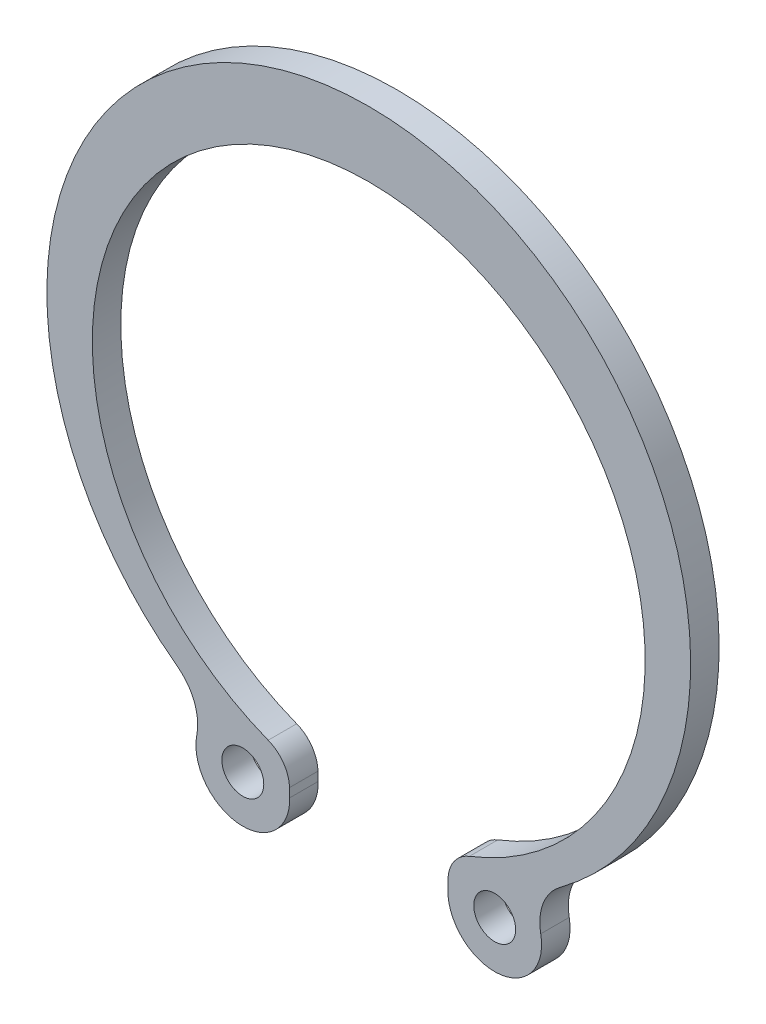
SolidWorks part; units mm, degrees
ref_plane "Спереди" through (0, 0, 0) normal (0, 0, 1) x (1, 0, 0)
ref_plane "Сверху" through (0, 0, 0) normal (0, 1, 0) x (1, 0, 0)
ref_plane "Справа" through (0, 0, 0) normal (1, 0, 0) x (0, 0, -1)
sketch "Эскиз1" plane through (0, 0, 0) normal (0, 0, 1) x (1, 0, 0)
  line L0 (0, -1000) -> (0, 49000) construction
  line L1 (5, -17.2154) -> (5, -16.6916)
  arc A0 (6.2265, -14.8472) -> (0, 16.1) centre (0, 0) ccw
  circle A2 centre (0, 0) radius 17.5 construction
  circle A3 centre (0, 0) radius 23.6 construction
  circle A4 centre (0, 0) radius 16.5 construction
  circle A5 centre (7.8, -17.2154) radius 1.25
  arc A7 (5, -17.2154) -> (10.5324, -16.6038) centre (7.8, -17.2154) ccw
  arc A8 (11.6077, -13.5886) -> (10.5324, -16.6038) centre (13.4599, -15.9485) ccw
  arc A9 (6.2265, -14.8472) -> (5, -16.6916) centre (7, -16.6916) ccw
  arc A10 (11.6077, -13.5886) -> (0, 20) centre (0, 1.2) ccw
  circle A12 centre (0, 1.2) radius 18.8 construction
  dimension "_d2" = 32.2
  dimension "_d3" = 37.6
  dimension "_d" = 35
  dimension "_D_" = 47.2
  dimension "_d1" = 33
  dimension "_d4" = 2.5
  dimension "_a" = 5.6
  dimension "_r1" = 3
  dimension "_r2" = 2
  dimension "_e" = 1.2
  dimension "_l" = 5
sketch "Эскиз2" plane through (0, 0, 0) normal (0, 0, 1) x (1, 0, 0)
  line L0 (0, -201000) -> (0, 249000) construction
  line L1 (0, -998.9795) -> (0, 49001.0205) construction
  line L2 (0, 0) -> (6.2265, -14.8472) construction
  line L3 (0, 0) -> (-6.0026, -15.3694) construction
  line L4 (0, 16.5) -> (0, 20.4)
  line L5 (6.2265, -14.8472) -> (5, -16.6916) construction
  line L6 (-6.0026, -15.3694) -> (-4.7308, -17.1829) construction
  line L7 (-4.7308, -17.1829) -> (-4.7178, -17.7065)
  line L8 (5, -17.2154) -> (5, -16.6916) construction
  line L9 (-11.4266, -14.2593) -> (-10.2657, -17.2426) construction
  line L10 (11.6077, -13.5886) -> (10.5324, -16.6038) construction
  line L11 (0, 20.4) -> (1.7, 20.4) construction
  arc A0 (0, 16.5) -> (-6.0026, -15.3694) centre (0, 0) ccw
  circle A1 centre (0, 0) radius 16.5 construction
  circle A2 centre (-7.517, -17.776) radius 1.25
  circle A3 centre (7.8, -17.2154) radius 1.25 construction
  arc A4 (-10.2657, -17.2426) -> (-4.7178, -17.7065) centre (-7.517, -17.776) ccw
  arc A5 (5, -17.2154) -> (10.5324, -16.6038) centre (7.8, -17.2154) ccw construction
  arc A6 (-6.0026, -15.3694) -> (-4.7308, -17.1829) centre (-6.7302, -17.2324) cw
  arc A7 (6.2265, -14.8472) -> (5, -16.6916) centre (7, -16.6916) ccw construction
  arc A8 (0, 20.4) -> (-11.4266, -14.2593) centre (0, 1.1868) ccw
  arc A9 (-10.2657, -17.2426) -> (-11.4266, -14.2593) centre (-13.2107, -16.6711) ccw
  arc A10 (11.6077, -13.5886) -> (10.5324, -16.6038) centre (13.4599, -15.9485) ccw construction
  dimension "D1" = 157.248
  dimension "D2" = 16.1
  dimension "D3" = 16.5
  dimension "D4" = 158.667
  dimension "_b" = 3.9
  dimension "_s" = 1.7
extrude "Бобышка-Вытянуть1" add sketch "Эскиз2" along normal blind 1.7
mirror "Зеркальное отражение1" about plane through (0, 16.5, 1.7) normal (-1, 0, 0) of bodies 103
sketch "Эскиз3" plane through (0, 0, 0) normal (0, 0, 1) x (1, 0, 0)
  circle A0 centre (0, 0) radius 16.5 construction
  circle A1 centre (0, 0) radius 23.6 construction
  circle A2 centre (0, 0) radius 16.5 construction
  circle A3 centre (0, 0) radius 23.6 construction
sketch "Эскиз4" plane through (0, 0, 0) normal (1, 0, 0) x (0, 0, -1)
  line L0 (-1.7, 20.4) -> (0.2, 20.4)
  dimension "_m" = 1.9
equation "\"D4@Эскиз2\"=\"D1@Эскиз2\"*\"D2@Эскиз2\"/\"D3@Эскиз2\""
equation "\"D1@Бобышка-Вытянуть1\"= \"_s@Эскиз2\""
